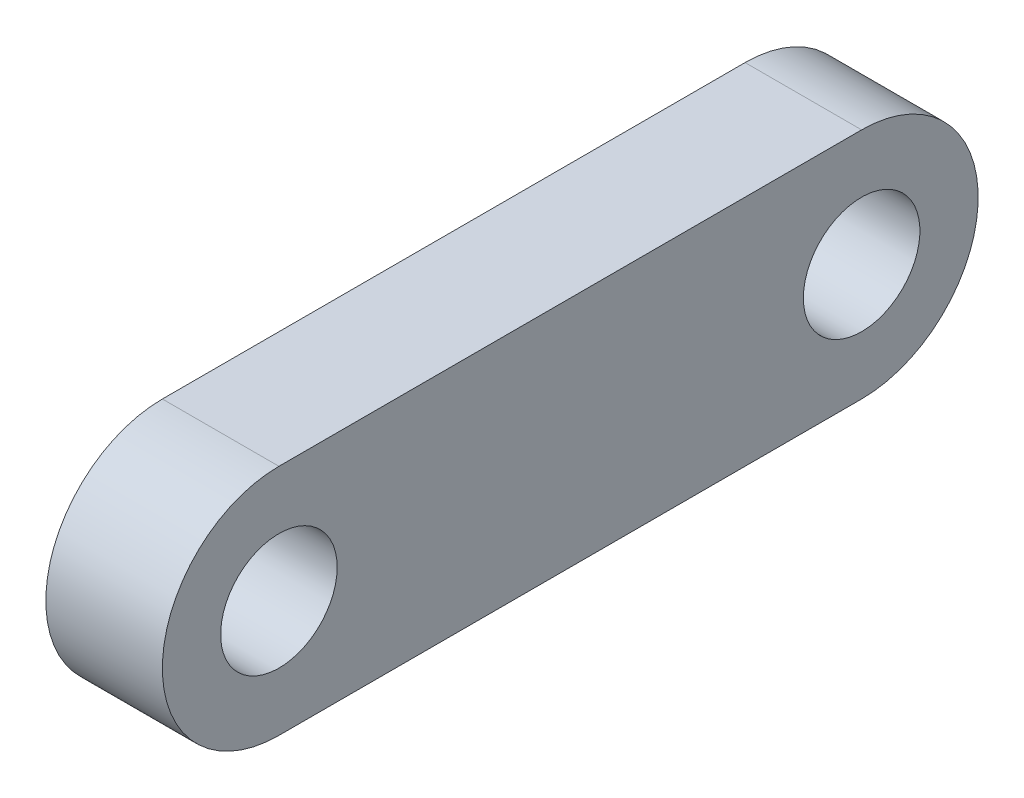
SolidWorks part; units mm, degrees
material "普通碳钢"
ref_plane "前视基准面" through (0, 0, 0) normal (0, 0, 1) x (1, 0, 0)
ref_plane "上视基准面" through (0, 0, 0) normal (0, 1, 0) x (1, 0, 0)
ref_plane "右视基准面" through (0, 0, 0) normal (1, 0, 0) x (0, 0, -1)
sketch "草图1" plane through (0, 0, 0) normal (1, 0, 0) x (0, 0, -1)
  line L0 (0, 28.2267) -> (0, -33.4957) construction
  line L1 (-74.8948, 0) -> (95.5944, 0) construction
  line L2 (20, 8) -> (-20, 8)
  line L3 (-20, -8) -> (20, -8)
  line L4 (74.8948, 0) -> (-95.5944, 0) construction
  arc A0 (-20, 8) -> (-20, -8) centre (-20, 0) ccw
  circle A1 centre (-20, 0) radius 4
  circle A2 centre (20, 0) radius 4
  arc A3 (20, 8) -> (20, -8) centre (20, 0) cw
  point P11 (0, 8)
  point P17 (0, -8)
  dimension "D1" = 8
  dimension "D2" = 8
  dimension "D3" = 40
extrude "凸台-拉伸1" add sketch "草图1" along normal blind 8
sketch3d "3D草图1"
  line L0 (8, 0, -20) -> (-16.6144, 0, -20) construction
  line L1 (8, 0, -20) -> (0, 0, -20) construction
